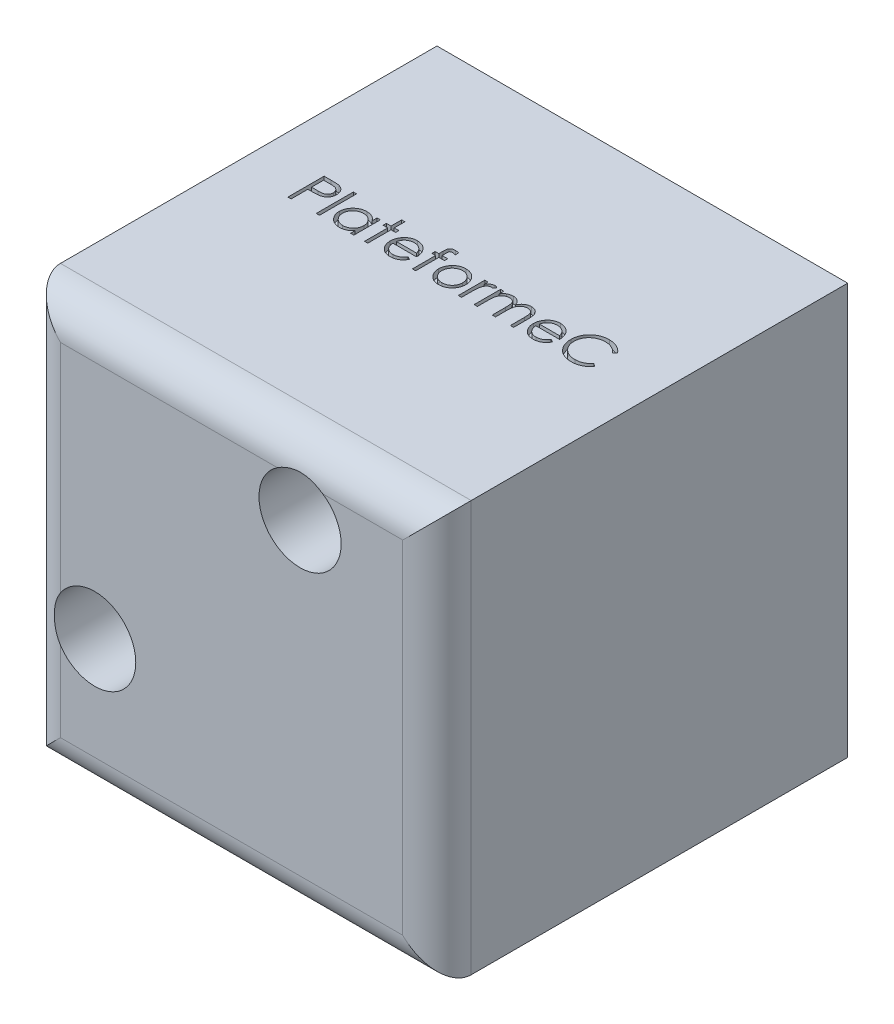
SolidWorks part; units mm, degrees
ref_plane "Plan de face" through (0, 0, 0) normal (0, 0, 1) x (1, 0, 0)
ref_plane "Plan de dessus" through (0, 0, 0) normal (0, 1, 0) x (1, 0, 0)
ref_plane "Plan de droite" through (0, 0, 0) normal (1, 0, 0) x (0, 0, -1)
sketch "Esquisse1" plane through (0, 0, 0) normal (0, 0, 1) x (1, 0, 0)
  line L1 (0, 0) -> (-60, 0)
  line L2 (0, 0) -> (0, 60)
  line L3 (0, 60) -> (-60, 60)
  line L4 (-60, 0) -> (-60, 60)
  dimension "D1" = 60
  dimension "D2" = 60
extrude "Boss.-Extru.1" add sketch "Esquisse1" along normal blind 60
sketch "Esquisse3" plane through (0, 0, 0) normal (0, 0, -1) x (-1, 0, 0)
  line L0 (60, 60) -> (60, 20)
  line L1 (60, 60) -> (60, 0) construction
  line L2 (60, 20) -> (58, 20)
  line L3 (58, 20) -> (58, 58)
  line L4 (58, 58) -> (20, 58)
  line L5 (20, 58) -> (20, 60)
  line L6 (0, 60) -> (60, 60) construction
  line L7 (20, 60) -> (60, 60)
  dimension "D1" = 40
  dimension "D2" = 40
  dimension "D3" = 2
  dimension "D4" = 2
extrude "Boss.-Extru.3" add sketch "Esquisse3" along normal blind 40
sketch "Esquisse6" plane through (-60, 0, 0) normal (-1, 0, 0) x (0, 0, 1)
  line L0 (30, 0) -> (30, 60) construction
  line L1 (60, 0) -> (0, 0) construction
  line L2 (60, 60) -> (-40, 60) construction
  text T0 "PING" font "Century Gothic" height in points 48
extrude "Enlèv. mat.-Extru.3" cut sketch "Esquisse6" against normal blind 1
sketch "Esquisse7" plane through (0, 60, 0) normal (0, 1, 0) x (1, 0, 0)
  line L0 (0, -30) -> (-60, -30) construction
  line L1 (0, -60) -> (0, 0) construction
  line L2 (-60, -60) -> (-60, 40) construction
  text T0 "PlateformeC" font "Century Gothic" height in points 20
extrude "Enlèv. mat.-Extru.4" cut sketch "Esquisse7" against normal blind 1
sketch "Esquisse8" plane through (-60, 0, 0) normal (-1, 0, 0) x (0, 0, 1)
  line L0 (-40, 20) -> (0, 60)
  line L1 (60, 60) -> (-40, 60) construction
  line L2 (0, 60) -> (-40, 60)
  line L3 (-40, 60) -> (-40, 20)
  dimension "D1" = 45
extrude "Enlèv. mat.-Extru.5" cut sketch "Esquisse8" against normal blind 2
sketch "Esquisse11" plane through (0, 60, 0) normal (0, 1, 0) x (1, 0, 0)
  line L0 (-20, 40) -> (-60, 0)
  line L1 (-60, 0) -> (-61.461, 41.461)
  line L2 (-61.461, 41.461) -> (-20, 40)
extrude "Enlèv. mat.-Extru.6" cut sketch "Esquisse11" against normal blind 2
fillet "Congé1" radius 5 4 edges at (-30, 0, 60) (0, 30, 60) (-60, 30, 60) (-30, 60, 60)
sketch "Esquisse13" plane through (0, 0, 60) normal (0, 0, 1) x (1, 0, 0)
  line L0 (-60, 60) -> (0, 60) construction
  line L1 (-60, 0) -> (-60, 60) construction
  circle A0 centre (-50, 20) radius 3
  circle A1 centre (-20, 50) radius 3
  dimension "D1" = 6
  dimension "D2" = 6
  dimension "D3" = 10
  dimension "D4" = 10
  dimension "D5" = 40
  dimension "D6" = 40
extrude "Enlèv. mat.-Extru.7" cut sketch "Esquisse13" against normal through all
sketch "Esquisse14" plane through (0, 0, 60) normal (0, 0, 1) x (1, 0, 0)
  circle A0 centre (-50, 20) radius 6
  circle A1 centre (-20, 50) radius 6
  dimension "D1" = 12
  dimension "D2" = 12
extrude "Enlèv. mat.-Extru.8" cut sketch "Esquisse14" against normal blind 54
sketch "Esquisse15" plane through (0, 0, 0) normal (0, -1, 0) x (1, 0, 0)
  line L1 (6.2592, -44.3072) -> (-60, -44.3072)
  line L2 (6.2592, -44.3072) -> (6.2592, 0)
  line L3 (6.2592, 0) -> (-60, 0)
  line L4 (-60, -44.3072) -> (-60, 0)
extrude "Enlèv. mat.-Extru.9" cut sketch "Esquisse15" against normal through all
